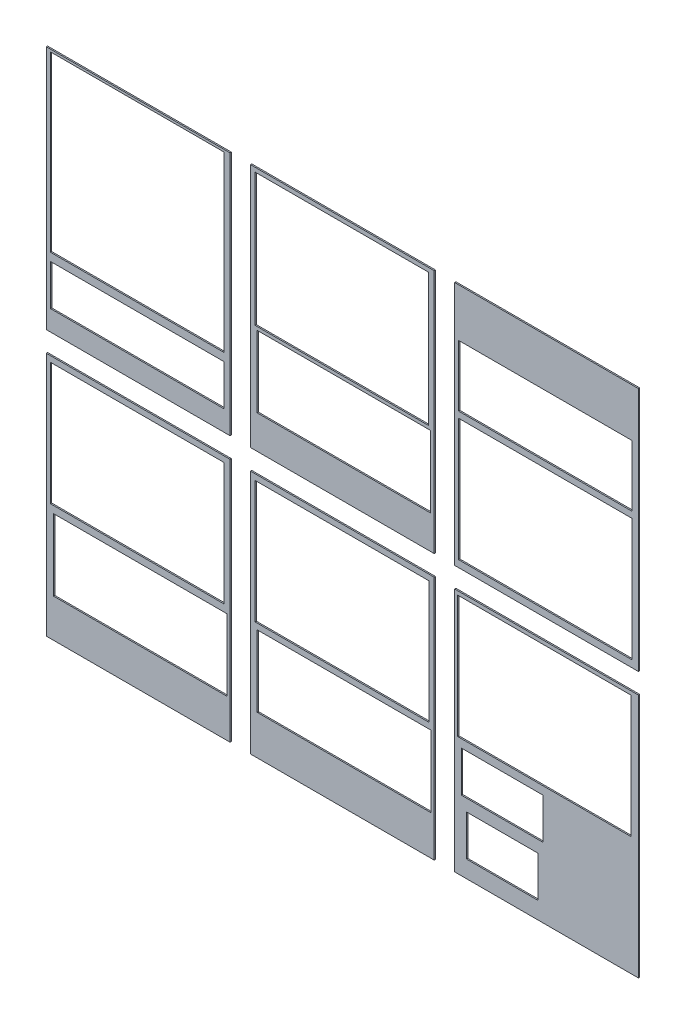
SolidWorks part; units mm, degrees
ref_plane "Front Plane" through (0, 0, 0) normal (0, 0, 1) x (1, 0, 0)
ref_plane "Top Plane" through (0, 0, 0) normal (0, 1, 0) x (1, 0, 0)
ref_plane "Right Plane" through (0, 0, 0) normal (1, 0, 0) x (0, 0, -1)
sketch "Sketch11" plane through (0, 0, 0) normal (0, 0, 1) x (1, 0, 0)
  line L0 (1856.1849, 582.6389) -> (1856.1849, -26.9611)
  line L1 (1348.1849, 582.6389) -> (1805.3849, 582.6389)
  line L2 (1348.1849, 582.6389) -> (1348.1849, -26.9611)
  line L3 (1348.1849, -26.9611) -> (1805.3849, -26.9611)
  line L4 (1805.3849, 582.6389) -> (1805.3849, -26.9611)
  line L5 (1348.1849, 582.6389) -> (1805.3849, -26.9611) construction
  line L6 (1348.1849, -26.9611) -> (1805.3849, 582.6389) construction
  line L7 (1856.1849, 582.6389) -> (2313.3849, 582.6389)
  line L8 (2313.3849, 582.6389) -> (2313.3849, -26.9611)
  line L9 (1856.1849, -26.9611) -> (2313.3849, -26.9611)
  line L10 (2364.1849, 582.6389) -> (2364.1849, -26.9611)
  line L11 (2364.1849, 582.6389) -> (2821.3849, 582.6389)
  line L12 (2821.3849, 582.6389) -> (2821.3849, -26.9611)
  line L13 (2364.1849, -26.9611) -> (2821.3849, -26.9611)
  line L14 (1856.1849, -77.7611) -> (1856.1849, -687.3611)
  line L15 (1856.1849, -77.7611) -> (2313.3849, -77.7611)
  line L16 (2313.3849, -77.7611) -> (2313.3849, -687.3611)
  line L17 (1856.1849, -687.3611) -> (2313.3849, -687.3611)
  line L18 (2364.1849, -77.7611) -> (2364.1849, -687.3611)
  line L19 (2364.1849, -77.7611) -> (2821.3849, -77.7611)
  line L20 (2821.3849, -77.7611) -> (2821.3849, -687.3611)
  line L21 (2364.1849, -687.3611) -> (2821.3849, -687.3611)
  line L30 (1348.1849, -77.7611) -> (1348.1849, -687.3611)
  line L31 (1348.1849, -77.7611) -> (1805.3849, -77.7611)
  line L32 (1805.3849, -77.7611) -> (1805.3849, -687.3611)
  line L33 (1348.1849, -687.3611) -> (1805.3849, -687.3611)
  line L38 (1856.1849, -738.1611) -> (1856.1849, -1347.7611) [skipped]
  line L39 (1856.1849, -738.1611) -> (2313.3849, -738.1611) [skipped]
  line L40 (2313.3849, -738.1611) -> (2313.3849, -1347.7611) [skipped]
  line L41 (1856.1849, -1347.7611) -> (2313.3849, -1347.7611) [skipped]
  line L42 (2364.1849, -738.1611) -> (2364.1849, -1347.7611) [skipped]
  line L43 (2364.1849, -738.1611) -> (2821.3849, -738.1611) [skipped]
  line L44 (2821.3849, -738.1611) -> (2821.3849, -1347.7611) [skipped]
  line L45 (2364.1849, -1347.7611) -> (2821.3849, -1347.7611) [skipped]
  line L46 (1348.1849, -738.1611) -> (1348.1849, -1347.7611) [skipped]
  line L47 (1348.1849, -738.1611) -> (1805.3849, -738.1611) [skipped]
  line L48 (1805.3849, -738.1611) -> (1805.3849, -1347.7611) [skipped]
  line L49 (1348.1849, -1347.7611) -> (1805.3849, -1347.7611) [skipped]
  point P0 (1576.7849, 277.8389)
  dimension "D1" = 457.2
  dimension "D2" = 609.6
  dimension "D3" = 3
  dimension "D4" = 3
extrude "Boss-Extrude1" add sketch "Sketch11" along normal blind 3.175
sketch "Top Base Layer, 17x13" plane through (0, 0, 0) normal (0, 0, 1) x (1, 0, 0)
  line L1 (1867.6012, 572.2866) -> (2299.4012, 572.2866)
  line L2 (1867.6012, 572.2866) -> (1867.6012, 242.0866)
  line L3 (1867.6012, 242.0866) -> (2299.4012, 242.0866)
  line L4 (2299.4012, 572.2866) -> (2299.4012, 242.0866)
  line L5 (1867.6012, 572.2866) -> (2299.4012, 242.0866) construction
  line L6 (1867.6012, 242.0866) -> (2299.4012, 572.2866) construction
  point P0 (2083.5012, 407.1866)
  point P5 (0, -44.249)
  point P6 (2083.5012, 407.1866)
  dimension "D1" = 431.8
  dimension "D2" = 330.2
sketch "Folder Inter Walls, 17x12" plane through (0, 0, 0) normal (0, 0, 1) x (1, 0, 0)
  line L0 (2371.5793, -391.9289) -> (2803.3793, -391.9289)
  line L1 (2373.6906, 295.0302) -> (2805.4906, 295.0302)
  line L2 (2373.6906, 295.0302) -> (2373.6906, -9.7698)
  line L3 (2373.6906, -9.7698) -> (2805.4906, -9.7698)
  line L4 (2805.4906, 295.0302) -> (2805.4906, -9.7698)
  line L5 (2373.6906, 295.0302) -> (2805.4906, -9.7698) construction
  line L6 (2373.6906, -9.7698) -> (2805.4906, 295.0302) construction
  line L7 (2371.5793, -87.1289) -> (2371.5793, -391.9289)
  line L8 (2803.3793, -87.1289) -> (2803.3793, -391.9289)
  line L9 (2371.5793, -87.1289) -> (2803.3793, -87.1289)
  line L10 (1358.1186, -92.1134) -> (1789.9186, -92.1134)
  line L11 (1358.1186, -92.1134) -> (1358.1186, -396.9134)
  line L12 (1789.9186, -92.1134) -> (1789.9186, -396.9134)
  line L13 (1358.1186, -396.9134) -> (1789.9186, -396.9134)
  line L14 (2299.7925, -92.1134) -> (2299.7925, -396.9134)
  line L15 (1867.9925, -396.9134) -> (2299.7925, -396.9134)
  line L16 (1867.9925, -92.1134) -> (2299.7925, -92.1134)
  line L17 (1867.9925, -92.1134) -> (1867.9925, -396.9134)
  point P0 (2589.5906, 142.6302)
  dimension "D1" = 304.8
  dimension "D2" = 431.8
sketch "Base Plate, 17x17" plane through (0, 0, 3.175) normal (0, 0, 1) x (1, 0, 0)
  line L1 (1358.0936, 576.7644) -> (1789.8936, 576.7644)
  line L2 (1358.0936, 576.7644) -> (1358.0936, 144.9644)
  line L3 (1358.0936, 144.9644) -> (1789.8936, 144.9644)
  line L4 (1789.8936, 576.7644) -> (1789.8936, 144.9644)
  line L5 (1358.0936, 576.7644) -> (1789.8936, 144.9644) construction
  line L6 (1358.0936, 144.9644) -> (1789.8936, 576.7644) construction
  point P0 (1573.9936, 360.8644)
  dimension "D1" = 431.8
  dimension "D2" = 431.8
extrude "Cut-Extrude2" cut sketch "Folder Inter Walls, 17x12" against normal through all both and the other way through all
extrude "Cut-Extrude3" cut sketch "Base Plate, 17x17" against normal through all both and the other way through all
extrude "Cut-Extrude4" cut sketch "Top Base Layer, 17x13" against normal through all both and the other way through all
sketch "Back Wall, 17x4" plane through (0, 0, 0) normal (0, 0, 1) x (1, 0, 0)
  line L1 (1358.6527, 125.1797) -> (1790.4527, 125.1797)
  line L2 (1358.6527, 125.1797) -> (1358.6527, 23.5797)
  line L3 (1358.6527, 23.5797) -> (1790.4527, 23.5797)
  line L4 (1790.4527, 125.1797) -> (1790.4527, 23.5797)
  line L5 (1358.6527, 125.1797) -> (1790.4527, 23.5797) construction
  line L6 (1358.6527, 23.5797) -> (1790.4527, 125.1797) construction
  point P0 (1574.5527, 74.3797)
  point P5 (0, 336.1857)
  point P6 (0, 279.4393)
  point P7 (1574.5527, 74.3797)
  dimension "D1" = 101.6
  dimension "D2" = 431.8
extrude "Cut-Extrude5" cut sketch "Back Wall, 17x4" against normal through all both and the other way through all
sketch "Angled Folder Wall 2, 17x7" plane through (0, 0, 0) normal (0, 0, 1) x (1, 0, 0)
  line L1 (1872.4735, 233.8644) -> (2304.2735, 233.8644)
  line L2 (1872.4735, 233.8644) -> (1872.4735, 56.0644)
  line L3 (1872.4735, 56.0644) -> (2304.2735, 56.0644)
  line L4 (2304.2735, 233.8644) -> (2304.2735, 56.0644)
  line L5 (1872.4735, 233.8644) -> (2304.2735, 56.0644) construction
  line L6 (1872.4735, 56.0644) -> (2304.2735, 233.8644) construction
  point P0 (2088.3735, 144.9644)
  point P5 (0, 628.8797)
  point P6 (0, 531.738)
  point P7 (0, 474.4997)
  point P8 (0, 445.6079)
  point P9 (2088.3735, 144.9644)
  dimension "D1" = 431.8
  dimension "D2" = 177.8
extrude "Cut-Extrude6" cut sketch "Angled Folder Wall 2, 17x7" against normal through all both and the other way through all
sketch "Front Wall, 17x6" plane through (0, 0, 0) normal (0, 0, 1) x (1, 0, 0)
  line L1 (2373.6906, 462.8112) -> (2805.4906, 462.8112)
  line L2 (2373.6906, 462.8112) -> (2373.6906, 310.4112)
  line L3 (2373.6906, 310.4112) -> (2805.4906, 310.4112)
  line L4 (2805.4906, 462.8112) -> (2805.4906, 310.4112)
  line L5 (2373.6906, 462.8112) -> (2805.4906, 310.4112) construction
  line L6 (2373.6906, 310.4112) -> (2805.4906, 462.8112) construction
  point P0 (2589.5906, 386.6112)
  point P5 (-557.9987, 55.4506)
  point P6 (-30.2193, -418.0306)
  point P7 (0, -503.487)
  point P8 (3.2708, -384.9218)
  point P9 (0, -402.911)
  point P10 (0, -316.0314)
  point P11 (2589.5906, 386.6112)
  dimension "D1" = 431.8
  dimension "D2" = 152.4
extrude "Cut-Extrude7" cut sketch "Front Wall, 17x6" against normal through all both and the other way through all
sketch "Left Wall, 16x8" plane through (0, 0, 0) normal (0, 0, 1) x (1, 0, 0)
  line L1 (1366.0234, -414.3501) -> (1797.8234, -414.3501)
  line L2 (1366.0234, -414.3501) -> (1366.0234, -592.1501)
  line L3 (1366.0234, -592.1501) -> (1797.8234, -592.1501)
  line L4 (1797.8234, -414.3501) -> (1797.8234, -592.1501)
  line L5 (1366.0234, -414.3501) -> (1797.8234, -592.1501) construction
  line L6 (1366.0234, -592.1501) -> (1797.8234, -414.3501) construction
  point P0 (1581.9234, -503.2501)
  point P5 (1581.9234, -503.2501)
  dimension "D1" = 431.8
  dimension "D2" = 177.8
extrude "Cut-Extrude8" cut sketch "Left Wall, 16x8" against normal through all both and the other way through all
sketch "Right wall, 12x8" plane through (0, 0, 0) normal (0, 0, 1) x (1, 0, 0)
  line L1 (1872.9719, -411.413) -> (2304.7719, -411.413)
  line L2 (1872.9719, -411.413) -> (1872.9719, -589.213)
  line L3 (1872.9719, -589.213) -> (2304.7719, -589.213)
  line L4 (2304.7719, -411.413) -> (2304.7719, -589.213)
  line L5 (1872.9719, -411.413) -> (2304.7719, -589.213) construction
  line L6 (1872.9719, -589.213) -> (2304.7719, -411.413) construction
  point P0 (2088.8719, -500.313)
  point P5 (373.9098, -54.2448)
  point P6 (334.9812, -60.2782)
  point P7 (331.0689, -13.2721)
  point P8 (2088.8719, -500.313)
  dimension "D1" = 177.8
  dimension "D2" = 431.8
extrude "Cut-Extrude9" cut sketch "Right wall, 12x8" against normal through all both and the other way through all
sketch "Angled Folder Wall 3, 8x4" plane through (0, 0, 0) normal (0, 0, 1) x (1, 0, 0)
  line L1 (2381.1169, -412.0825) -> (2584.3169, -412.0825)
  line L2 (2381.1169, -412.0825) -> (2381.1169, -513.6825)
  line L3 (2381.1169, -513.6825) -> (2584.3169, -513.6825)
  line L4 (2584.3169, -412.0825) -> (2584.3169, -513.6825)
  line L5 (2381.1169, -412.0825) -> (2584.3169, -513.6825) construction
  line L6 (2381.1169, -513.6825) -> (2584.3169, -412.0825) construction
  point P0 (2482.7169, -462.8825)
  point P5 (648.4513, 0)
  point P6 (675.3208, 165.822)
  point P7 (2482.7169, -462.8825)
  dimension "D1" = 101.6
  dimension "D2" = 203.2
extrude "Cut-Extrude10" cut sketch "Angled Folder Wall 3, 8x4" against normal through all both and the other way through all
sketch "Angled folder wall 1, 7x4" plane through (0, 0, 0) normal (0, 0, 1) x (1, 0, 0)
  line L1 (2393.8169, -543.4012) -> (2571.6169, -543.4012)
  line L2 (2393.8169, -543.4012) -> (2393.8169, -645.0012)
  line L3 (2393.8169, -645.0012) -> (2571.6169, -645.0012)
  line L4 (2571.6169, -543.4012) -> (2571.6169, -645.0012)
  line L5 (2393.8169, -543.4012) -> (2571.6169, -645.0012) construction
  line L6 (2393.8169, -645.0012) -> (2571.6169, -543.4012) construction
  point P0 (2482.7169, -594.2012)
  point P5 (-556.2153, 155.9026)
  point P6 (2482.7169, -594.2012)
  dimension "D1" = 101.6
  dimension "D2" = 177.8
extrude "Cut-Extrude11" cut sketch "Angled folder wall 1, 7x4" against normal through all both and the other way through all
